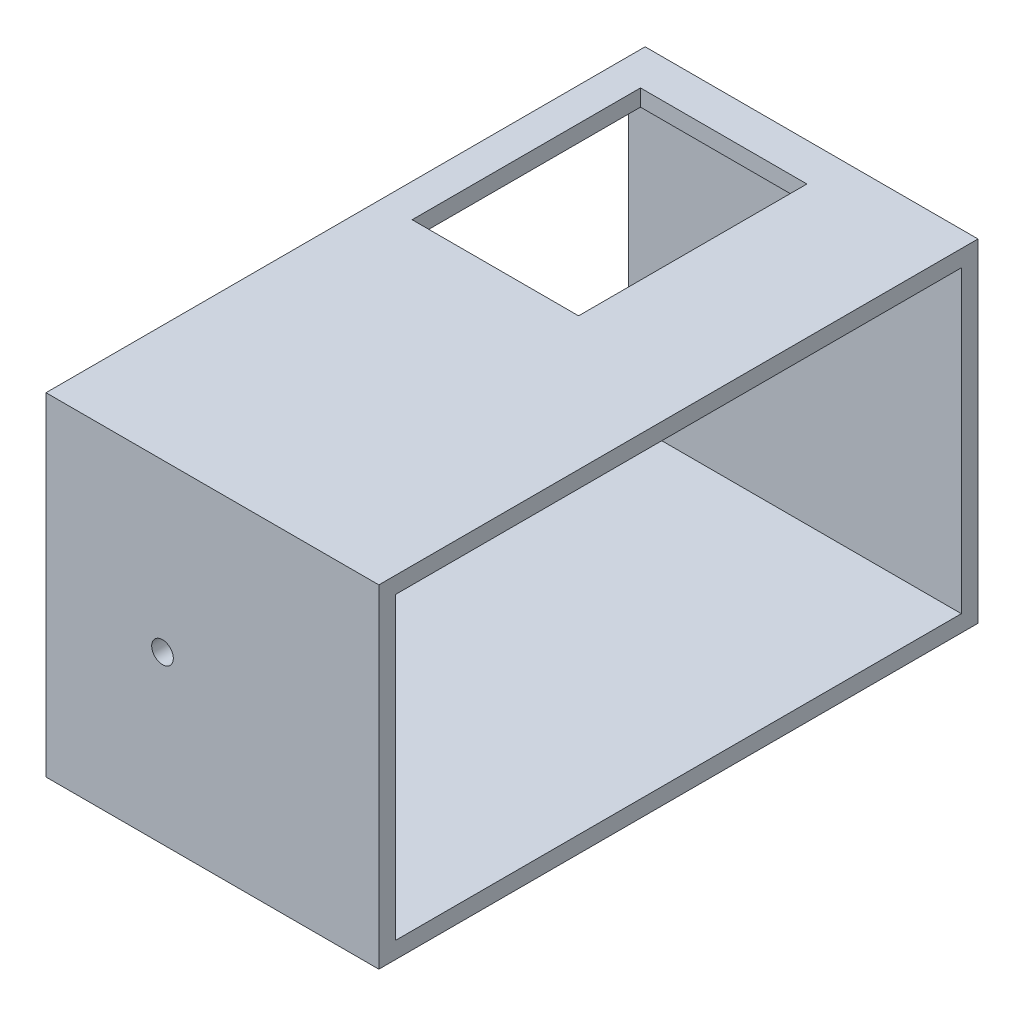
SolidWorks part; units mm, degrees
ref_plane "前视基准面" through (0, 0, 0) normal (0, 0, 1) x (1, 0, 0)
ref_plane "上视基准面" through (0, 0, 0) normal (0, 1, 0) x (1, 0, 0)
ref_plane "右视基准面" through (0, 0, 0) normal (1, 0, 0) x (0, 0, -1)
sketch "草图1" plane through (0, 0, 0) normal (0, 1, 0) x (1, 0, 0)
  line L1 (-50, 90) -> (50, 90)
  line L2 (-50, 90) -> (-50, -90)
  line L3 (-50, -90) -> (50, -90)
  line L4 (50, 90) -> (50, -90)
  line L5 (-50, 90) -> (50, -90) construction
  line L6 (-50, -90) -> (50, 90) construction
  point P0 (0, 0)
  dimension "D1" = 180
  dimension "D2" = 100
extrude "凸台-拉伸1" add sketch "草图1" along normal blind 100
sketch "草图2" plane through (0, 100, 0) normal (0, 1, 0) x (1, 0, 0)
  line L0 (50, 90) -> (-50, 90) construction
  line L1 (-40, 78.6) -> (10, 78.6)
  line L2 (-40, 78.6) -> (-40, 10)
  line L3 (-40, 10) -> (10, 10)
  line L4 (10, 78.6) -> (10, 10)
  line L5 (-50, 90) -> (-50, -90) construction
  dimension "D1" = 50
  dimension "D2" = 68.6
  dimension "D3" = 11.4
  dimension "D4" = 10
extrude "切除-拉伸1" cut sketch "草图2" against normal blind 90
sketch "草图3" plane through (-50, 0, 0) normal (-1, 0, 0) x (0, 0, 1)
  line L0 (-90, 100) -> (90, 100) construction
  line L1 (-85, 95) -> (85, 95)
  line L2 (-85, 95) -> (-85, 5)
  line L3 (-85, 5) -> (85, 5)
  line L4 (85, 95) -> (85, 5)
  line L5 (-90, 100) -> (-90, 0) construction
  line L6 (-90, 0) -> (90, 0) construction
  line L7 (90, 100) -> (90, 0) construction
  dimension "D1" = 5
  dimension "D2" = 5
  dimension "D3" = 5
  dimension "D4" = 5
extrude "切除-拉伸2" cut sketch "草图3" against normal through all
sketch "草图4" plane through (0, 0, 90) normal (0, 0, 1) x (1, 0, 0)
  line L0 (-50, 100) -> (-50, 0) construction
  line L1 (-50, 100) -> (50, 100) construction
  circle A0 centre (-15, 50) radius 3.25
  dimension "D1" = 6.5
  dimension "D2" = 35
  dimension "D3" = 50
extrude "切除-拉伸3" cut sketch "草图4" against normal through all both and the other way through all
